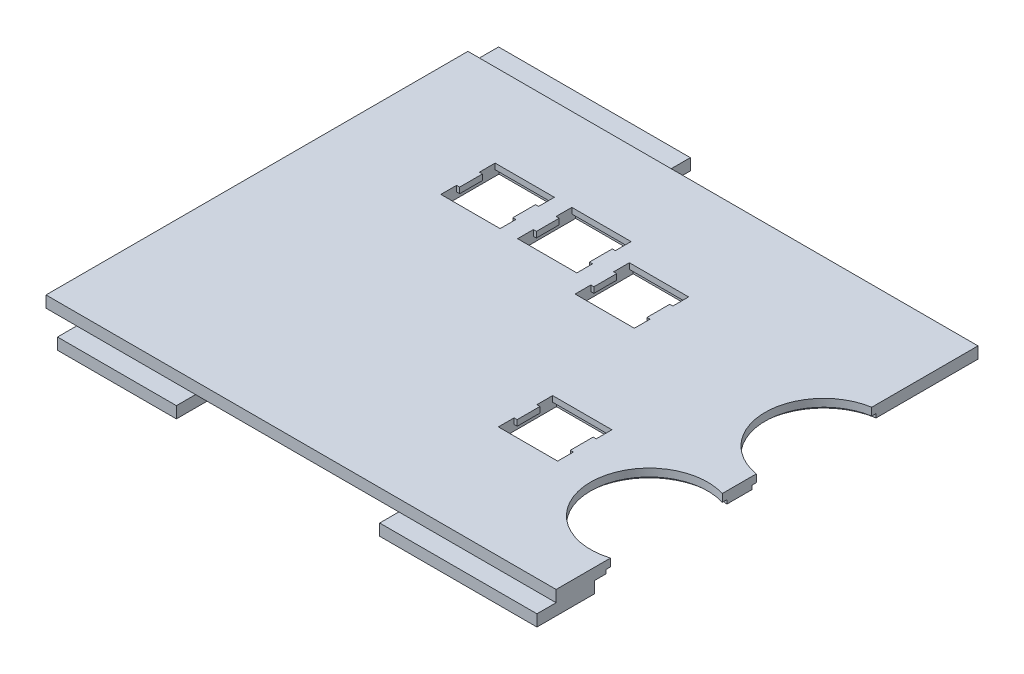
SolidWorks part; units mm, degrees
ref_plane "Front Plane" through (0, 0, 0) normal (0, 0, 1) x (1, 0, 0)
ref_plane "Top Plane" through (0, 0, 0) normal (0, 1, 0) x (1, 0, 0)
ref_plane "Right Plane" through (0, 0, 0) normal (1, 0, 0) x (0, 0, -1)
sketch "Sketch1" plane through (0, 0, 0) normal (0, 1, 0) x (1, 0, 0)
  line L1 (0, 0) -> (133, 0)
  line L2 (0, 0) -> (0, 110)
  line L3 (0, 110) -> (133, 110)
  line L4 (133, 0) -> (133, 110)
  dimension "D1" = 110
  dimension "D2" = 133
extrude "Boss-Extrude1" add sketch "Sketch1" along normal blind 3
sketch "Sketch2" plane through (0, 0, 0) normal (0, -1, 0) x (1, 0, 0)
  line L0 (133, 0) -> (133, -110) construction
  line L1 (0, -118) -> (50, -118)
  line L2 (0, -118) -> (0, -100)
  line L3 (0, -100) -> (50, -100)
  line L4 (50, -118) -> (50, -100)
  line L5 (133, -110) -> (0, -110) construction
  line L6 (133, -10) -> (92, -10)
  line L7 (133, -10) -> (133, 5)
  line L8 (133, 5) -> (92, 5)
  line L9 (8, -10) -> (8, 5)
  line L10 (0, -110) -> (0, 0) construction
  line L11 (0, 0) -> (133, 0) construction
  line L12 (39, -10) -> (39, 5)
  line L13 (92, -10) -> (92, 5)
  line L14 (0, -110) -> (0, 0) construction
  line L15 (39, -10) -> (8, -10)
  line L16 (39, 5) -> (8, 5)
  point P22 (133, -2.5)
  dimension "D1" = 10
  dimension "D2" = 18
  dimension "D3" = 50
  dimension "D4" = 15
  dimension "D5" = 10
  dimension "D6" = 8
  dimension "D7" = 39
  dimension "D8" = 41
extrude "Boss-Extrude2" add sketch "Sketch2" along normal blind 3
sketch "Sketch3" plane through (0, 3, 0) normal (0, 1, 0) x (1, 0, 0)
  line L2 (133, 110) -> (0, 110) construction
  line L3 (0, 0) -> (133, 0) construction
  line L4 (0, 110) -> (0, 0) construction
  circle A1 centre (128.5, 28.75) radius 15.25
  circle A2 centre (135.5, 67.25) radius 15.25
  dimension "D1" = 42.75
  dimension "D4" = 30.5
  dimension "D5" = 128.5
  dimension "D2" = 28.75
  dimension "D3" = 7
extrude "Cut-Extrude1" cut sketch "Sketch3" against normal up to next
sketch "Sketch4" plane through (0, 0, 0) normal (0, -1, 0) x (1, 0, 0)
  circle A0 centre (128.5, -28.75) radius 16.375
  circle A1 centre (135.5, -67.25) radius 16.375
  point P6 (0, 0)
  point P7 (0, 0)
  dimension "D1" = 32.75
extrude "Cut-Extrude2" cut sketch "Sketch4" against normal blind 1
sketch "Sketch6" plane through (0, 3, 0) normal (0, 1, 0) x (1, 0, 0)
  line L5 (29.575, 84.225) -> (29.575, 78.275)
  line L8 (43.425, 84.225) -> (43.425, 78.275)
  line L14 (36.5, 88.325) -> (36.5, 81.25) construction
  line L104 (49.575, 84.225) -> (49.575, 78.275)
  line L125 (63.425, 84.225) -> (63.425, 78.275)
  line L146 (56.5, 88.325) -> (56.5, 81.25) construction
  line L157 (48.775, 88.325) -> (64.225, 88.325)
  line L160 (28.775, 88.325) -> (44.225, 88.325)
  line L162 (29.575, 84.225) -> (28.775, 84.225)
  line L163 (28.775, 84.225) -> (28.775, 88.325)
  line L164 (44.225, 88.325) -> (44.225, 84.225)
  line L165 (44.225, 84.225) -> (43.425, 84.225)
  line L166 (29.575, 81.25) -> (43.425, 81.25) construction
  line L167 (44.225, 78.275) -> (43.425, 78.275)
  line L168 (44.225, 74.175) -> (44.225, 78.275)
  line L169 (28.775, 78.275) -> (28.775, 74.175)
  line L170 (29.575, 78.275) -> (28.775, 78.275)
  line L171 (28.775, 74.175) -> (44.225, 74.175)
  line L172 (49.575, 84.225) -> (48.775, 84.225)
  line L173 (48.775, 84.225) -> (48.775, 88.325)
  line L174 (64.225, 88.325) -> (64.225, 84.225)
  line L175 (64.225, 84.225) -> (63.425, 84.225)
  line L176 (49.575, 81.25) -> (63.425, 81.25) construction
  line L177 (64.225, 78.275) -> (63.425, 78.275)
  line L178 (64.225, 74.175) -> (64.225, 78.275)
  line L179 (48.775, 78.275) -> (48.775, 74.175)
  line L180 (49.575, 78.275) -> (48.775, 78.275)
  line L181 (48.775, 74.175) -> (64.225, 74.175)
  line L182 (69.575, 79.225) -> (69.575, 73.275)
  line L183 (83.425, 79.225) -> (83.425, 73.275)
  line L184 (76.5, 83.325) -> (76.5, 76.25) construction
  line L185 (68.775, 83.325) -> (84.225, 83.325)
  line L186 (69.575, 79.225) -> (68.775, 79.225)
  line L187 (68.775, 79.225) -> (68.775, 83.325)
  line L188 (84.225, 83.325) -> (84.225, 79.225)
  line L189 (84.225, 79.225) -> (83.425, 79.225)
  line L190 (69.575, 76.25) -> (83.425, 76.25) construction
  line L191 (84.225, 73.275) -> (83.425, 73.275)
  line L192 (84.225, 69.175) -> (84.225, 73.275)
  line L193 (68.775, 73.275) -> (68.775, 69.175)
  line L194 (69.575, 73.275) -> (68.775, 73.275)
  line L195 (68.775, 69.175) -> (84.225, 69.175)
  line L196 (89.575, 39.225) -> (89.575, 33.275)
  line L197 (103.425, 39.225) -> (103.425, 33.275)
  line L198 (96.5, 43.325) -> (96.5, 36.25) construction
  line L199 (88.775, 43.325) -> (104.225, 43.325)
  line L200 (89.575, 39.225) -> (88.775, 39.225)
  line L201 (88.775, 39.225) -> (88.775, 43.325)
  line L202 (104.225, 43.325) -> (104.225, 39.225)
  line L203 (104.225, 39.225) -> (103.425, 39.225)
  line L204 (89.575, 36.25) -> (103.425, 36.25) construction
  line L205 (104.225, 33.275) -> (103.425, 33.275)
  line L206 (104.225, 29.175) -> (104.225, 33.275)
  line L207 (88.775, 33.275) -> (88.775, 29.175)
  line L208 (89.575, 33.275) -> (88.775, 33.275)
  line L209 (88.775, 29.175) -> (104.225, 29.175)
  point P0 (0, 0)
  point P3 (36.5, 88.325)
  point P17 (56.5, 88.325)
  point P35 (76.5, 83.325)
  point P52 (96.5, 43.325)
  dimension "D1" = 0.8
  dimension "D2" = 5.95
  dimension "D3" = 0.8
  dimension "D4" = 15.45
  dimension "D5" = 4.1
  dimension "D6" = 4.1
  dimension "D7" = 0.8
  dimension "D8" = 5.95
  dimension "D9" = 0.8
  dimension "D10" = 15.45
  dimension "D11" = 4.1
  dimension "D12" = 0.8
  dimension "D13" = 5.95
  dimension "D14" = 0.8
  dimension "D15" = 15.45
  dimension "D16" = 4.1
  dimension "D17" = 0.8
  dimension "D18" = 5.95
  dimension "D19" = 0.8
  dimension "D20" = 15.45
  dimension "D21" = 20
  dimension "D22" = 20
  dimension "D23" = 20
  dimension "D24" = 40
  dimension "D25" = 5.95
  dimension "D26" = 5.95
  dimension "D27" = 5.95
  dimension "D28" = 5.95
  dimension "D29" = 32
  dimension "D30" = 14
  dimension "D31" = 5
extrude "Cut-Extrude3" cut sketch "Sketch6" against normal through all
sketch "Sketch7" plane through (0, 0, 0) normal (0, -1, 0) x (1, 0, 0)
  line L0 (84.225, -83.325) -> (84.225, -79.225) construction
  line L17 (84.225, -84.325) -> (68.775, -84.325)
  line L18 (84.225, -84.325) -> (84.225, -68.175)
  line L19 (84.225, -68.175) -> (68.775, -68.175)
  line L20 (68.775, -84.325) -> (68.775, -68.175)
  line L21 (68.775, -79.225) -> (68.775, -83.325) construction
  line L22 (68.775, -83.325) -> (84.225, -83.325) construction
  line L23 (84.225, -69.175) -> (68.775, -69.175) construction
  line L33 (104.225, -43.325) -> (104.225, -39.225) construction
  line L34 (104.225, -44.325) -> (88.775, -44.325)
  line L35 (104.225, -44.325) -> (104.225, -28.175)
  line L36 (104.225, -28.175) -> (88.775, -28.175)
  line L37 (88.775, -44.325) -> (88.775, -28.175)
  line L38 (88.775, -39.225) -> (88.775, -43.325) construction
  line L39 (88.775, -43.325) -> (104.225, -43.325) construction
  line L40 (104.225, -29.175) -> (88.775, -29.175) construction
  line L41 (44.225, -88.325) -> (44.225, -84.225) construction
  line L42 (64.225, -89.325) -> (48.775, -89.325)
  line L43 (64.225, -89.325) -> (64.225, -73.175)
  line L44 (64.225, -73.175) -> (48.775, -73.175)
  line L45 (48.775, -89.325) -> (48.775, -73.175)
  line L46 (44.225, -89.325) -> (28.775, -89.325)
  line L47 (44.225, -89.325) -> (44.225, -73.175)
  line L48 (44.225, -73.175) -> (28.775, -73.175)
  line L49 (28.775, -89.325) -> (28.775, -73.175)
  line L50 (28.775, -84.225) -> (28.775, -88.325) construction
  line L51 (64.225, -88.325) -> (64.225, -84.225) construction
  line L52 (48.775, -84.225) -> (48.775, -88.325) construction
  line L53 (48.775, -88.325) -> (64.225, -88.325) construction
  line L54 (64.225, -74.175) -> (48.775, -74.175) construction
  line L55 (28.775, -88.325) -> (44.225, -88.325) construction
  line L56 (44.225, -74.175) -> (28.775, -74.175) construction
  dimension "D1" = 1
  dimension "D2" = 1
  dimension "D4" = 1
  dimension "D5" = 1
  dimension "D6" = 1
  dimension "D3" = 1
  dimension "D7" = 1
  dimension "D8" = 1
extrude "Cut-Extrude4" cut sketch "Sketch7" against normal blind 1.5
